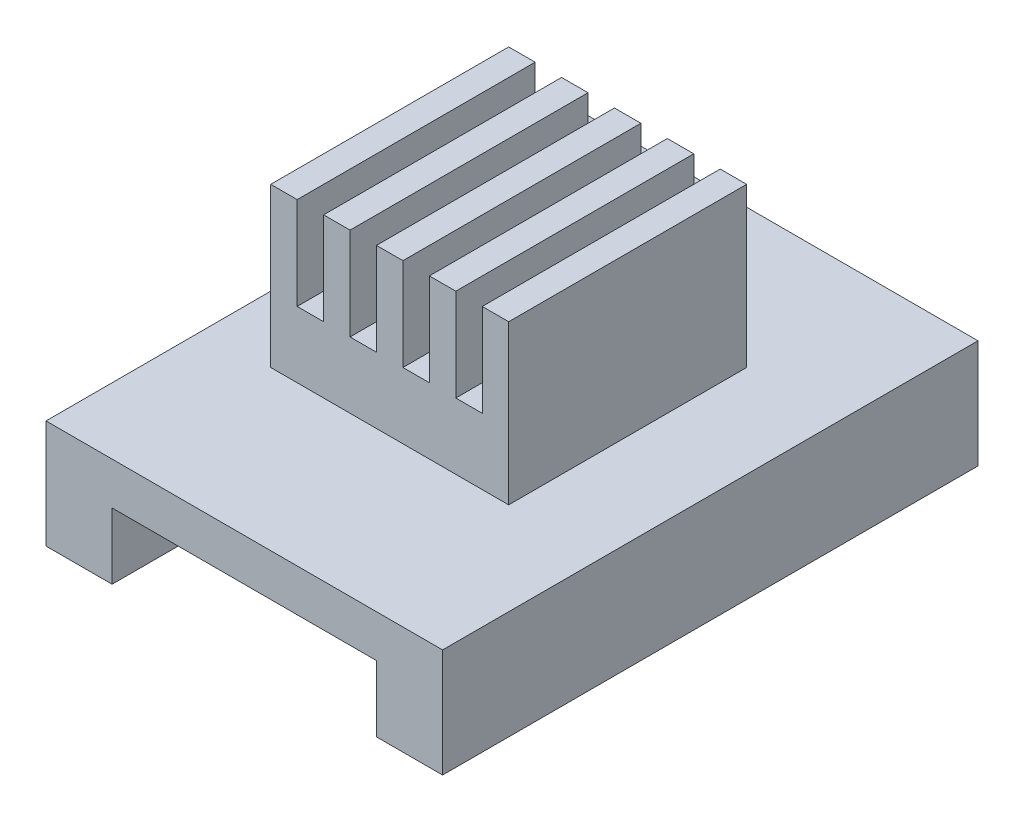
SolidWorks part; units mm, degrees
ref_plane "Front Plane" through (0, 0, 0) normal (0, 0, 1) x (1, 0, 0)
ref_plane "Top Plane" through (0, 0, 0) normal (0, 1, 0) x (1, 0, 0)
ref_plane "Right Plane" through (0, 0, 0) normal (1, 0, 0) x (0, 0, -1)
sketch "Sketch1" plane through (0, 0, 0) normal (0, 1, 0) x (1, 0, 0)
  line L1 (0, 0) -> (15, 0)
  line L2 (0, 0) -> (0, 20.25)
  line L3 (0, 20.25) -> (15, 20.25)
  line L4 (15, 0) -> (15, 20.25)
  line L5 (0, 0) -> (15, 20.25) construction
  line L6 (0, 20.25) -> (15, 0) construction
  point P4 (7.5, 10.125)
  dimension "D1" = 15
  dimension "D2" = 20.25
extrude "Boss-Extrude1" add sketch "Sketch1" along normal blind 1.6
sketch "Sketch2" plane through (0, 0, 0) normal (0, -1, 0) x (1, 0, 0)
  line L0 (15, -20.25) -> (0, -20.25) construction
  line L1 (0, 0) -> (2.5, 0)
  line L2 (0, 0) -> (0, -20.25)
  line L3 (0, -20.25) -> (2.5, -20.25)
  line L4 (2.5, 0) -> (2.5, -20.25)
  line L5 (0, 0) -> (2.5, -20.25) construction
  line L6 (0, -20.25) -> (2.5, 0) construction
  line L8 (15, 0) -> (12.5, 0)
  line L9 (15, 0) -> (15, -20.25)
  line L10 (15, -20.25) -> (12.5, -20.25)
  line L11 (12.5, 0) -> (12.5, -20.25)
  line L12 (15, 0) -> (12.5, -20.25) construction
  line L13 (15, -20.25) -> (12.5, 0) construction
  point P4 (1.25, -10.125)
  point P12 (13.75, -10.125)
  dimension "D1" = 2.5
  dimension "D2" = 2.5
extrude "Boss-Extrude2" add sketch "Sketch2" along normal blind 2.5
sketch "Sketch3" plane through (0, 1.6, 0) normal (0, 1, 0) x (1, 0, 0)
  line L0 (0, 0) -> (15, 0) construction
  line L1 (2.5, 6) -> (11.5, 6)
  line L2 (2.5, 6) -> (2.5, 15)
  line L3 (2.5, 15) -> (11.5, 15)
  line L4 (11.5, 6) -> (11.5, 15)
  line L5 (2.5, 6) -> (11.5, 15) construction
  line L6 (2.5, 15) -> (11.5, 6) construction
  line L7 (0, 20.25) -> (0, 0) construction
  point P4 (7, 10.5)
  dimension "D1" = 9
  dimension "D2" = 9
  dimension "D3" = 6
  dimension "D4" = 2.5
extrude "Boss-Extrude3" add sketch "Sketch3" along normal blind 6
sketch "Sketch4" plane through (0, 0, -6) normal (0, 0, 1) x (1, 0, 0)
  line L0 (2.5, 7.6) -> (11.5, 7.6) construction
  line L1 (3.5, 7.6) -> (4.5, 7.6)
  line L2 (3.5, 7.6) -> (3.5, 4.1)
  line L3 (3.5, 4.1) -> (4.5, 4.1)
  line L4 (4.5, 7.6) -> (4.5, 4.1)
  line L5 (3.5, 7.6) -> (4.5, 4.1) construction
  line L6 (3.5, 4.1) -> (4.5, 7.6) construction
  line L7 (2.5, 7.6) -> (2.5, 1.6) construction
  line L8 (5.5, 7.6) -> (6.5, 7.6)
  line L9 (5.5, 7.6) -> (5.5, 4.1)
  line L10 (5.5, 4.1) -> (6.5, 4.1)
  line L11 (6.5, 7.6) -> (6.5, 4.1)
  line L12 (5.5, 7.6) -> (6.5, 4.1) construction
  line L13 (5.5, 4.1) -> (6.5, 7.6) construction
  line L14 (7.5, 7.6) -> (8.5, 7.6)
  line L15 (7.5, 7.6) -> (7.5, 4.1)
  line L16 (7.5, 4.1) -> (8.5, 4.1)
  line L17 (8.5, 7.6) -> (8.5, 4.1)
  line L18 (7.5, 7.6) -> (8.5, 4.1) construction
  line L19 (7.5, 4.1) -> (8.5, 7.6) construction
  line L20 (9.5, 7.6) -> (10.5, 7.6)
  line L21 (9.5, 7.6) -> (9.5, 4.1)
  line L22 (9.5, 4.1) -> (10.5, 4.1)
  line L23 (10.5, 7.6) -> (10.5, 4.1)
  line L24 (9.5, 7.6) -> (10.5, 4.1) construction
  line L25 (9.5, 4.1) -> (10.5, 7.6) construction
  point P4 (4, 5.85)
  point P11 (6, 5.85)
  point P16 (8, 5.85)
  point P21 (10, 5.85)
  dimension "D1" = 1
  dimension "D2" = 1
  dimension "D3" = 1
  dimension "D4" = 1
  dimension "D5" = 1
  dimension "D6" = 3.5
extrude "Cut-Extrude1" cut sketch "Sketch4" against normal up to next
